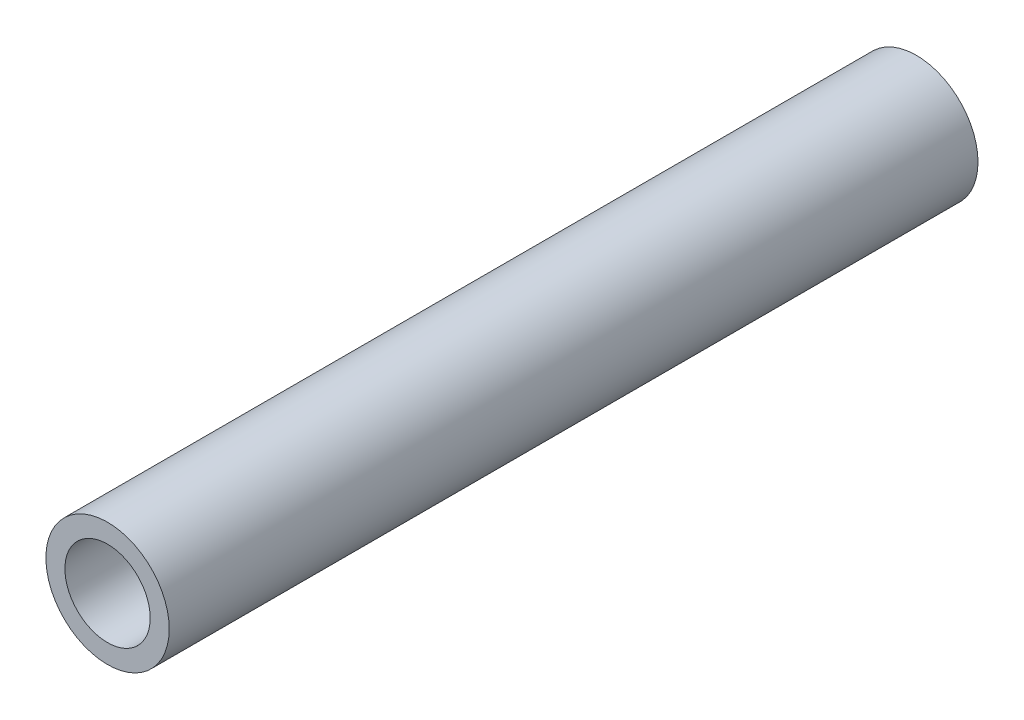
SolidWorks part; units mm, degrees
material "PVC Rigid"
ref_plane "Front Plane" through (0, 0, 0) normal (0, 0, 1) x (1, 0, 0)
ref_plane "Top Plane" through (0, 0, 0) normal (0, 1, 0) x (1, 0, 0)
ref_plane "Right Plane" through (0, 0, 0) normal (1, 0, 0) x (0, 0, -1)
sketch "Sketch1" plane through (0, 0, 0) normal (0, 0, 1) x (1, 0, 0)
  circle A0 centre (0, 0) radius 7.747
  circle A1 centre (0, 0) radius 5.3594
  dimension "D1" = 15.494
  dimension "D2" = 10.7188
extrude "Boss-Extrude1" add sketch "Sketch1" along normal blind 101.6
